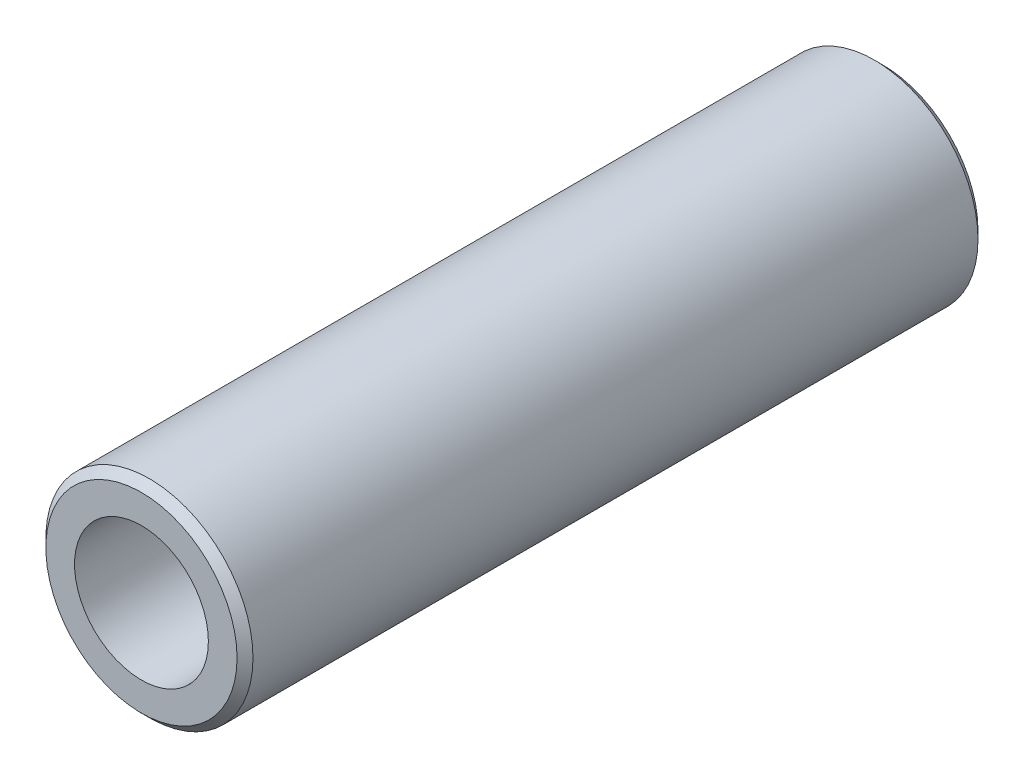
SolidWorks part; units mm, degrees
material "1.1191 (C45E)"
ref_plane "Piano frontale" through (0, 0, 0) normal (0, 0, 1) x (1, 0, 0)
ref_plane "Piano superiore" through (0, 0, 0) normal (0, 1, 0) x (1, 0, 0)
ref_plane "Piano destro" through (0, 0, 0) normal (1, 0, 0) x (0, 0, -1)
sketch "Schizzo2" plane through (0, 0, 0) normal (0, 0, 1) x (1, 0, 0)
  circle A0 centre (0, 0) radius 4.2
  circle A1 centre (0, 0) radius 6.5
  dimension "D1" = 2.3
  dimension "D2" = 13
extrude "Estrusione-Estrusione1" add sketch "Schizzo2" along normal blind 46.5
chamfer "Smusso1" distance 0.5 angle 45 2 edges at (6.5, 0, 46.5) (6.5, 0, 0)
